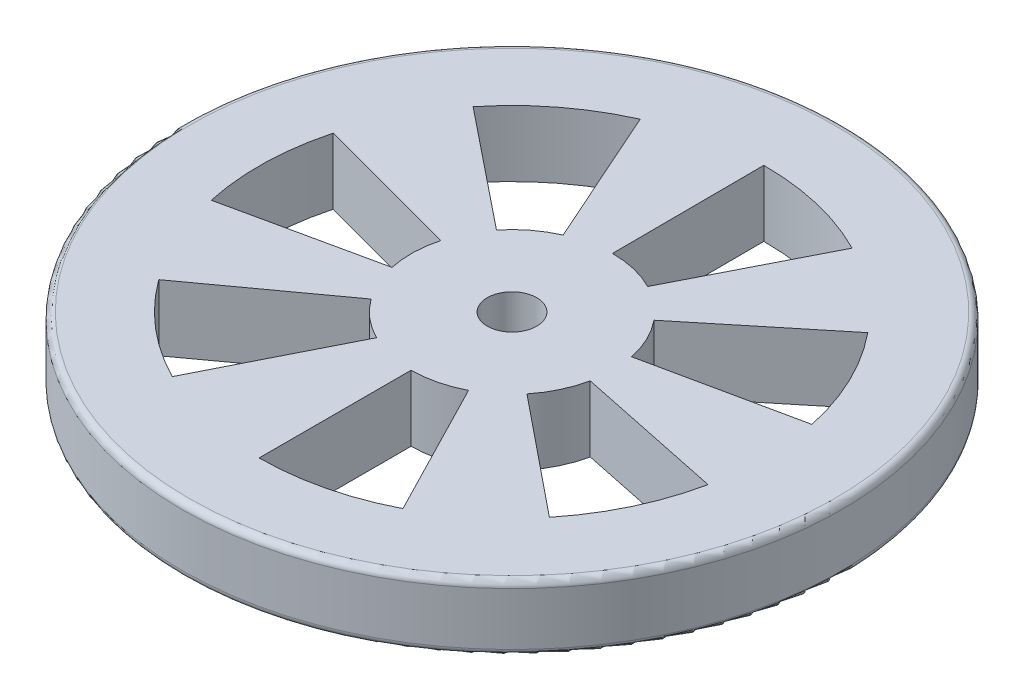
SolidWorks part; units mm, degrees
ref_plane "Front Plane" through (0, 0, 0) normal (0, 0, 1) x (1, 0, 0)
ref_plane "Top Plane" through (0, 0, 0) normal (0, 1, 0) x (1, 0, 0)
ref_plane "Right Plane" through (0, 0, 0) normal (1, 0, 0) x (0, 0, -1)
sketch "Sketch1" plane through (0, 0, 0) normal (0, 1, 0) x (1, 0, 0)
  circle A0 centre (0, 0) radius 100
  dimension "D1" = 200
extrude "Boss-Extrude1" add sketch "Sketch1" along normal blind 20
fillet "Fillet1" radius 2 2 edges at (0, 0, 100) (0, 20, 100)
sketch "Sketch2" plane through (0, 20, 0) normal (0, 1, 0) x (1, 0, 0)
  circle A0 centre (0, 0) radius 7.5
  dimension "D1" = 15
extrude "Cut-Extrude1" cut sketch "Sketch2" against normal through all
sketch "Sketch3" plane through (0, 0, 0) normal (0, -1, 0) x (1, 0, 0)
  line L0 (0, 30.6177) -> (0, 76.7321)
  line L1 (14.0177, 27.2204) -> (35.1302, 68.2179)
  arc A0 (14.0177, 27.2204) -> (0, 30.6177) centre (0, 0) ccw
  arc A1 (35.1302, 68.2179) -> (0, 76.7321) centre (0, 0) ccw
extrude "Cut-Extrude2" cut sketch "Sketch3" against normal through all
pattern_circular "CirPattern1" count 7 every 51 about axis through (0, 0, 0) along (0, 1, 0) of "Cut-Extrude2"
